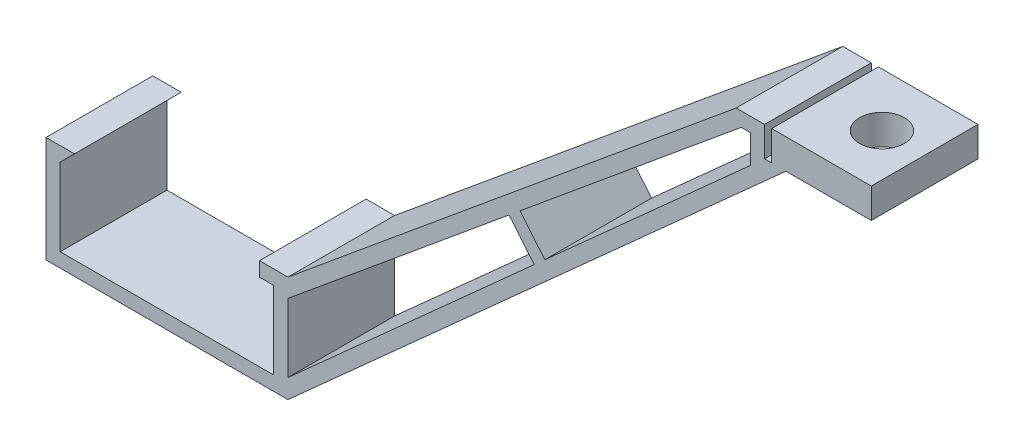
SolidWorks part; units mm, degrees
ref_plane "Front Plane" through (0, 0, 0) normal (0, 0, 1) x (1, 0, 0)
ref_plane "Top Plane" through (0, 0, 0) normal (0, 1, 0) x (1, 0, 0)
ref_plane "Right Plane" through (0, 0, 0) normal (1, 0, 0) x (0, 0, -1)
sketch "Sketch1" plane through (0, 0, 0) normal (0, 0, 1) x (1, 0, 0)
  line L0 (-15, 4.085) -> (-15, 15) construction
  line L1 (15, -15) -> (-15, -15) construction
  line L2 (15, -15) -> (15, -4.085) construction
  line L3 (15, 15) -> (-15, 15) construction
  line L4 (-15, -15) -> (-15, -4.085) construction
  line L5 (15, -15) -> (-15, 15) construction
  line L6 (15, 15) -> (-15, -15) construction
  line L7 (-15, 4.085) -> (-10, 4.085) construction
  line L9 (-15, -4.085) -> (-10, -4.085) construction
  line L10 (-10, 4.085) -> (-10, -4.085) construction
  line L11 (15, -4.085) -> (10, -4.085) construction
  line L13 (15, 4.085) -> (10, 4.085) construction
  line L14 (10, -4.085) -> (10, 4.085) construction
  line L15 (15, 4.085) -> (15, 15) construction
  line L16 (-15, -15) -> (-15, -4.085)
  line L25 (15, -4.085) -> (13, -4.085)
  line L26 (15, -15) -> (15, -4.085)
  line L27 (15, -15) -> (-15, -15)
  line L28 (-10, 4.085) -> (-10, -4.085) construction
  line L29 (-15, 4.085) -> (-10, 4.085) construction
  line L30 (-15, 4.085) -> (-15, 15) construction
  line L31 (15, 15) -> (-15, 15) construction
  line L32 (15, 4.085) -> (15, 15) construction
  line L33 (15, 4.085) -> (10, 4.085) construction
  line L34 (10, -4.085) -> (10, 4.085) construction
  line L35 (17, -2.085) -> (13, -2.085)
  line L36 (17, -17) -> (17, -2.085)
  line L37 (17, -17) -> (-17, -17)
  line L38 (-17, -17) -> (-17, -2.085)
  line L39 (-17, -2.085) -> (-13, -2.085)
  line L40 (13, -2.085) -> (13, -4.085)
  line L41 (-15, -4.085) -> (-13, -2.085)
  line L42 (-17, -2.085) -> (-10, -2.085) construction
  line L43 (-15, -4.085) -> (-10, -4.085) construction
  line L44 (17, -2.085) -> (10, -2.085) construction
  line L45 (15, -4.085) -> (10, -4.085) construction
  point P0 (0, 0)
  point P14 (-10, 0)
  point P15 (10, 0)
  dimension "D1" = 30
  dimension "D2" = 30
  dimension "D3" = 8.17
  dimension "D4" = 5
  dimension "D7" = 2
  dimension "D8" = 225
  dimension "D5" = 0
  dimension "D6" = 2
extrude "Boss-Extrude1" add sketch "Sketch1" along normal blind 15
sketch "Sketch2" plane through (0, 0, 0) normal (0, 0, -1) x (-1, 0, 0)
  line L0 (-15, -4.085) -> (-80, 50) construction
  line L1 (-80, 50) -> (-84, 50) construction
  line L2 (-85, 50) -> (-85, 86) construction
  line L3 (-85, 86) -> (-80, 86) construction
  line L4 (-80, 86) -> (-80, 84) construction
  line L5 (-80, 84) -> (-84, 84) construction
  line L6 (-84, 84) -> (-84, 52) construction
  line L7 (-84, 52) -> (-80, 52) construction
  line L8 (-80, 52) -> (-80, 50) construction
  line L9 (-85, 50) -> (-85, 45.8) construction
  line L10 (-85, 45.8) -> (-84, 45.8) construction
  line L11 (-84, 45.8) -> (-84, 50) construction
  line L12 (-80, 50) -> (-17, -2.085)
  line L13 (-80, 50) -> (-84, 50)
  line L14 (-87, 50) -> (-87, 45.8)
  line L15 (-87, 45.8) -> (-17, -17)
  line L16 (-17, -2.085) -> (-17, -4.68)
  line L17 (-80.7197, 48) -> (-49.6306, 22.2972)
  line L19 (-82, 44.0012) -> (-53.1128, 18.0852)
  line L22 (-80.7197, 48) -> (-85, 48) construction
  line L23 (-85, 46.6926) -> (-19, -12.5188) construction
  line L24 (-85, 48) -> (-85, 46.6926) construction
  line L25 (-80.7197, 48) -> (-82, 48)
  line L26 (-82, 48) -> (-82, 44.0012)
  line L27 (-80.7197, 48) -> (-19, -3.0265) construction
  line L28 (-19, -3.0265) -> (-19, -12.5188) construction
  line L29 (-17, -14.3131) -> (-17, -17)
  line L30 (-17, -2.085) -> (-17, -17) construction
  line L31 (-85, 50) -> (-85, 45.8)
  line L32 (-85, 45.8) -> (-84, 45.8)
  line L33 (-84, 45.8) -> (-84, 50)
  line L34 (-85, 50) -> (-87, 50)
  line L35 (-80, 50) -> (-87, 50) construction
  line L36 (-48.8598, 21.66) -> (-52.3678, 17.4169) construction
  line L37 (-49.6306, 22.2972) -> (-53.1128, 18.0852)
  line L38 (-48.0891, 21.0228) -> (-51.6229, 16.7486)
  line L39 (-49.6306, 22.2972) -> (-53.1385, 18.0541) construction
  line L40 (-48.0891, 21.0228) -> (-51.5971, 16.7797) construction
  line L41 (-51.6229, 16.7486) -> (-17, -14.3131)
  line L42 (-48.0891, 21.0228) -> (-17, -4.68)
  line L43 (-48.8598, 21.66) -> (-52.3678, 17.4169) construction
  dimension "D1" = 65
  dimension "D2" = 35
  dimension "D3" = 32
  dimension "D4" = 2
  dimension "D5" = 2
  dimension "D6" = 1
  dimension "D7" = 4
  dimension "D8" = 4.2
  dimension "D9" = 2
  dimension "D11" = 2
  dimension "D10" = 2
  dimension "D12" = 0
  dimension "D13" = 1
  dimension "D14" = 1
extrude "Boss-Extrude2" add sketch "Sketch2" against normal up to surface (15 mm away)
sketch "Sketch3" plane through (0, 0, 0) normal (0, 0, -1) x (-1, 0, 0)
  line L0 (-87, 50) -> (-87, 45.8) construction
  line L1 (-87, 50) -> (-99, 50)
  line L2 (-87, 50) -> (-87, 45.8)
  line L3 (-87, 45.8) -> (-99, 45.8)
  line L4 (-99, 50) -> (-99, 45.8)
  line L5 (-87, 45.8) -> (-17, -17) construction
  dimension "D1" = 12
extrude "Boss-Extrude3" add sketch "Sketch3" against normal up to surface (15 mm away)
sketch "Sketch4" plane through (0, 50, 0) normal (0, 1, 0) x (1, 0, 0)
  line L0 (93, -15) -> (93, 0) construction
  line L2 (85, 0) -> (99, 0) construction
  line L3 (99, -15) -> (99, 0) construction
  line L4 (99, -15) -> (85, -15) construction
  circle A0 centre (93, -7.5) radius 3.15
  dimension "D1" = 6.3
  dimension "D2" = 6
extrude "Cut-Extrude1" cut sketch "Sketch4" against normal up to next
